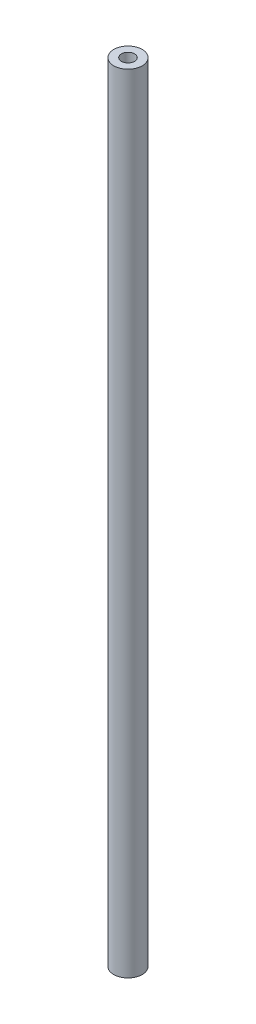
SolidWorks part; units mm, degrees
ref_plane "Front Plane" through (0, 0, 0) normal (0, 0, 1) x (1, 0, 0)
ref_plane "Top Plane" through (0, 0, 0) normal (0, 1, 0) x (1, 0, 0)
ref_plane "Right Plane" through (0, 0, 0) normal (1, 0, 0) x (0, 0, -1)
sketch "Sketch1" plane through (0, 0, 0) normal (0, 1, 0) x (1, 0, 0)
  circle A0 centre (0, 0) radius 1.95
  dimension "D1" = 3.9
extrude "Boss-Extrude1" add sketch "Sketch1" along normal blind 108
sketch "Sketch2" plane through (0, 108, 0) normal (0, 1, 0) x (1, 0, 0)
  circle A0 centre (0, 0) radius 0.9
  dimension "D1" = 1.8
extrude "Cut-Extrude1" cut sketch "Sketch2" against normal blind 112
